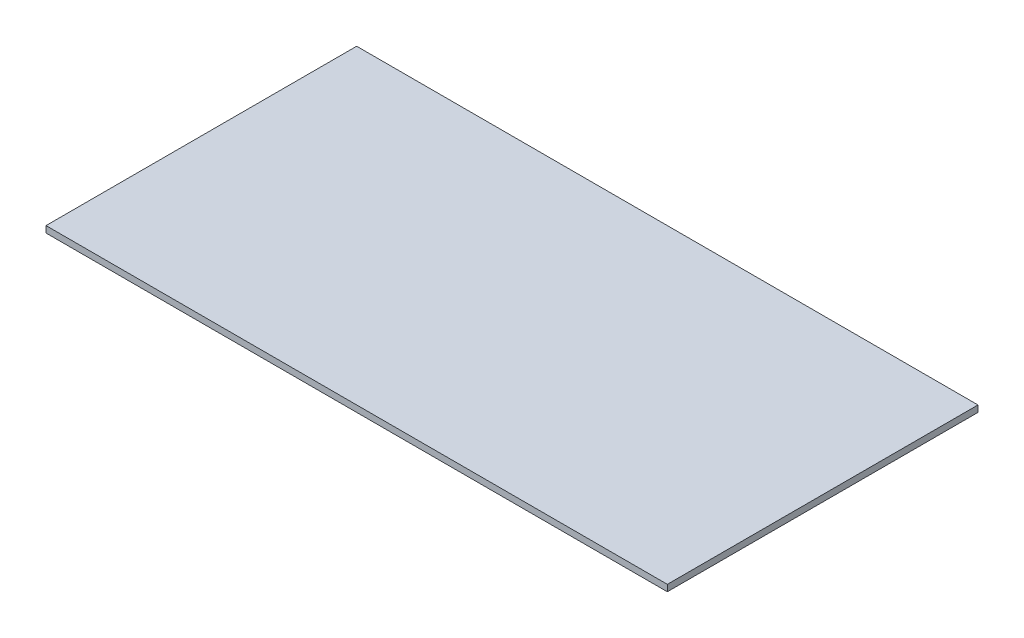
SolidWorks part; units mm, degrees
ref_plane "Front Plane" through (0, 0, 0) normal (0, 0, 1) x (1, 0, 0)
ref_plane "Top Plane" through (0, 0, 0) normal (0, 1, 0) x (1, 0, 0)
ref_plane "Right Plane" through (0, 0, 0) normal (1, 0, 0) x (0, 0, -1)
sketch "Sketch1" plane through (0, 0, 0) normal (0, 1, 0) x (1, 0, 0)
  line L1 (0, 0) -> (1219.2, 0)
  line L2 (0, 0) -> (0, 609.6)
  line L3 (0, 609.6) -> (1219.2, 609.6)
  line L4 (1219.2, 0) -> (1219.2, 609.6)
extrude "Boss-Extrude1" add sketch "Sketch1" along normal blind 12.7
